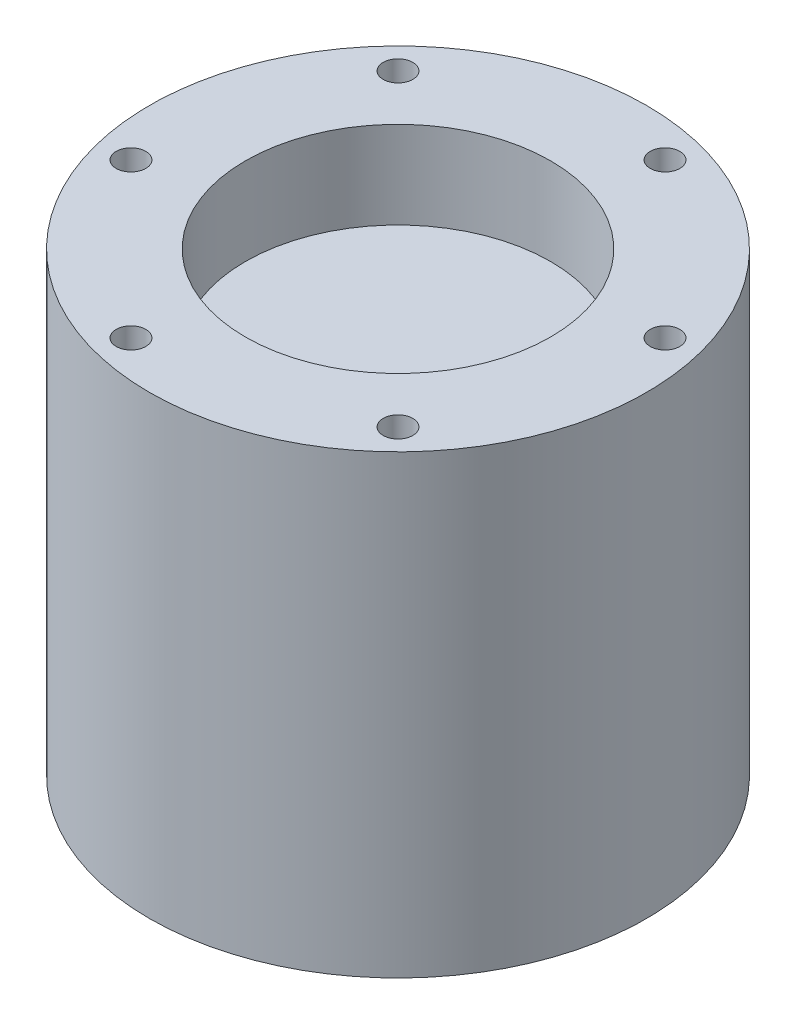
SolidWorks part; units mm, degrees
ref_plane "前视基准面" through (0, 0, 0) normal (0, 0, 1) x (1, 0, 0)
ref_plane "上视基准面" through (0, 0, 0) normal (0, 1, 0) x (1, 0, 0)
ref_plane "右视基准面" through (0, 0, 0) normal (1, 0, 0) x (0, 0, -1)
sketch "草图1" plane through (0, 0, 0) normal (0, 1, 0) x (1, 0, 0)
  circle A0 centre (0, 0) radius 28.5
  circle A1 centre (0, 0) radius 19 construction
  circle A2 centre (0, 19) radius 1.5 construction
  circle A3 centre (19, 0) radius 1.5 construction
  circle A4 centre (0, -19) radius 1.5 construction
  circle A5 centre (-19, 0) radius 1.5 construction
  point P15 (0, 0)
  dimension "D1" = 57
  dimension "D3" = 3
  dimension "D4" = 38
  dimension "D2" = 4
extrude "凸台-拉伸1" add sketch "草图1" along normal blind 52.25
sketch "草图3" plane through (0, 52.25, 0) normal (0, 1, 0) x (1, 0, 0)
  circle A0 centre (0, 0) radius 17.5
  dimension "D1" = 35
extrude "切除-拉伸2" cut sketch "草图3" against normal blind 10
sketch "草图4" plane through (0, 52.25, 0) normal (0, 1, 0) x (1, 0, 0)
  line L0 (0, 0) -> (22.7752, -22.7752) construction
  line L1 (0, 0) -> (0, -30.3748) construction
  circle A0 centre (0, 0) radius 25 construction
  circle A1 centre (17.6777, -17.6777) radius 1.7
  circle A2 centre (-6.4705, -24.1481) radius 1.7
  circle A3 centre (-24.1481, -6.4705) radius 1.7
  circle A4 centre (-17.6777, 17.6777) radius 1.7
  circle A5 centre (6.4705, 24.1481) radius 1.7
  circle A6 centre (24.1481, 6.4705) radius 1.7
  point P6 (17.6777, -17.6777)
  point P7 (17.6777, -17.6777)
  point P8 (17.6777, -17.6777)
  point P17 (0, 0)
  point P21 (0, 0)
  point P22 (17.6777, -17.6777)
  dimension "D1" = 50
  dimension "D2" = 3.4
  dimension "D4" = 45
  dimension "D3" = 6
extrude "切除-拉伸3" cut sketch "草图4" against normal blind 10
sketch "草图5" plane through (0, 0, 0) normal (0, -1, 0) x (1, 0, 0)
  circle A0 centre (0, 0) radius 19 construction
  circle A1 centre (0, -19) radius 1.5
  circle A2 centre (-19, 0) radius 1.5
  circle A3 centre (0, 19) radius 1.5
  circle A4 centre (19, 0) radius 1.5
  point P13 (0, 0)
  dimension "D1" = 38
  dimension "D2" = 3
  dimension "D3" = 4
extrude "切除-拉伸4" cut sketch "草图5" against normal blind 10
